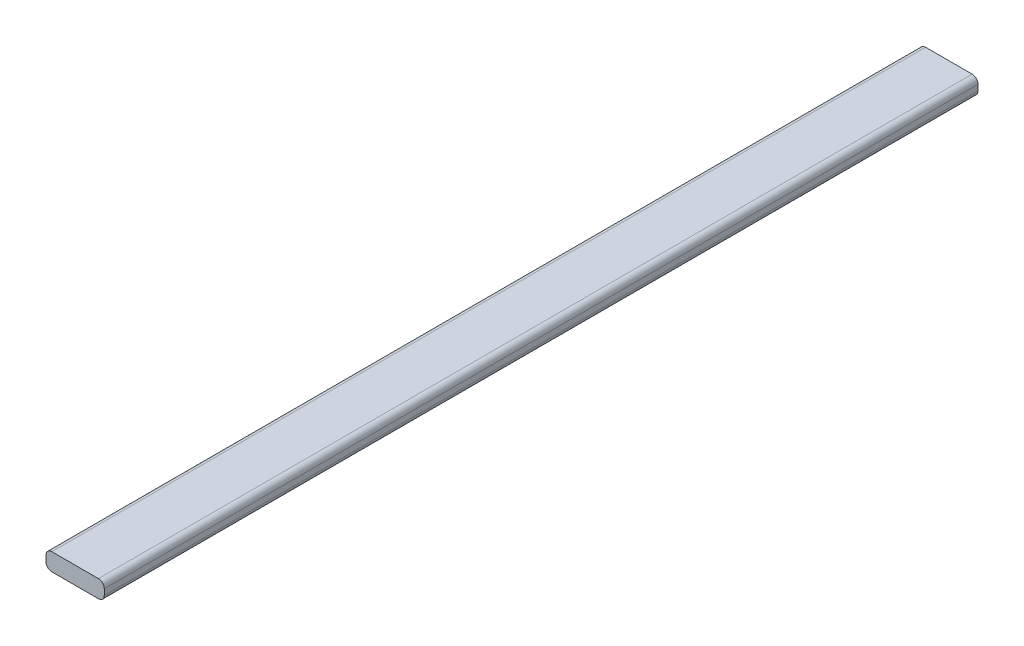
SolidWorks part; units mm, degrees
ref_plane "Plan de face" through (0, 0, 0) normal (0, 0, 1) x (1, 0, 0)
ref_plane "Plan de dessus" through (0, 0, 0) normal (0, 1, 0) x (1, 0, 0)
ref_plane "Plan de droite" through (0, 0, 0) normal (1, 0, 0) x (0, 0, -1)
sketch "Esquisse1" plane through (0, 0, 0) normal (0, 0, 1) x (1, 0, 0)
  line L1 (-4, 1.5) -> (4, 1.5)
  line L2 (-5, 0.5) -> (-5, -0.5)
  line L3 (-4, -1.5) -> (4, -1.5)
  line L4 (5, 0.5) -> (5, -0.5)
  arc A0 (4, 1.5) -> (5, 0.5) centre (4, 0.5) cw
  arc A1 (4, -1.5) -> (5, -0.5) centre (4, -0.5) ccw
  arc A2 (-5, -0.5) -> (-4, -1.5) centre (-4, -0.5) ccw
  arc A3 (-4, 1.5) -> (-5, 0.5) centre (-4, 0.5) ccw
  point P4 (-5, 0)
  point P5 (0, 1.5)
  point P6 (0, 0)
  point P8 (0, 0)
  point P11 (5, 1.5)
  point P16 (-5, -1.5)
  point P19 (-5, 1.5)
  dimension "D3" = 1
  dimension "D1" = 10
  dimension "D2" = 3
extrude "Boss.-Extru.1" add sketch "Esquisse1" along normal blind 150
